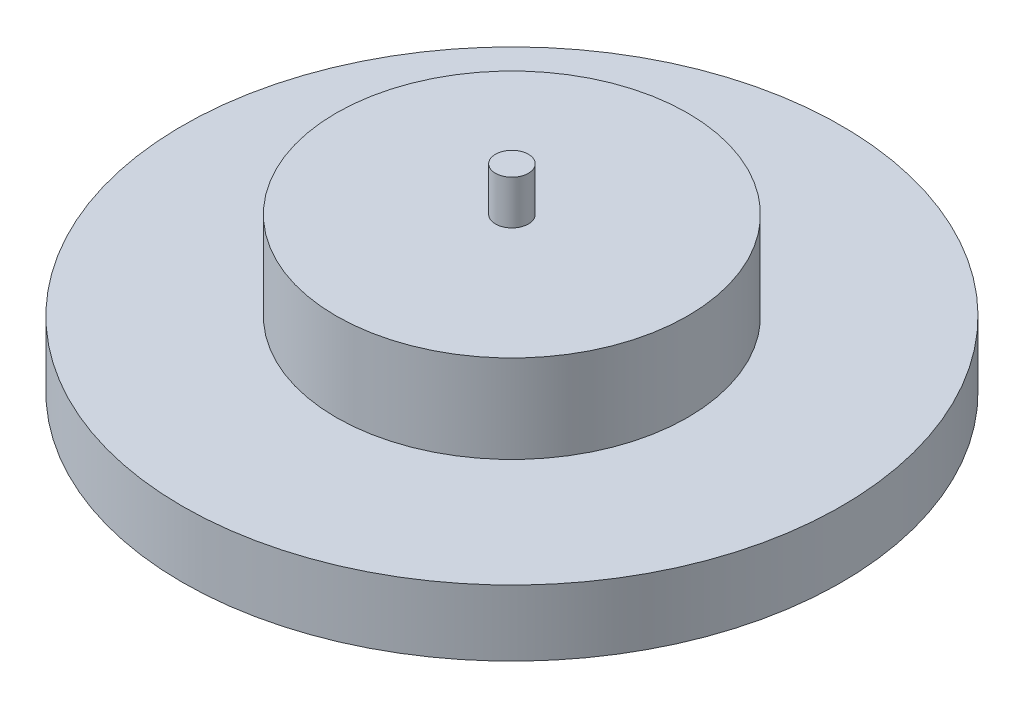
SolidWorks part; units mm, degrees
ref_plane "前视基准面" through (0, 0, 0) normal (0, 0, 1) x (1, 0, 0)
ref_plane "上视基准面" through (0, 0, 0) normal (0, 1, 0) x (1, 0, 0)
ref_plane "右视基准面" through (0, 0, 0) normal (1, 0, 0) x (0, 0, -1)
other "Configuration Table"
sketch "草图1" plane through (0, 0, 0) normal (0, 1, 0) x (1, 0, 0)
  circle A0 centre (0, 0) radius 15
  dimension "D1" = 30
extrude "凸台-拉伸1" add sketch "草图1" along normal blind 3
sketch "草图2" plane through (0, 3, 0) normal (0, 1, 0) x (1, 0, 0)
  circle A0 centre (0, 0) radius 8
  dimension "D1" = 16
extrude "凸台-拉伸2" add sketch "草图2" along normal blind 4
sketch "草图3" plane through (0, 7, 0) normal (0, 1, 0) x (1, 0, 0)
  circle A0 centre (0, 0) radius 0.75
  dimension "D1" = 1.5
extrude "凸台-拉伸3" add sketch "草图3" along normal blind 2
